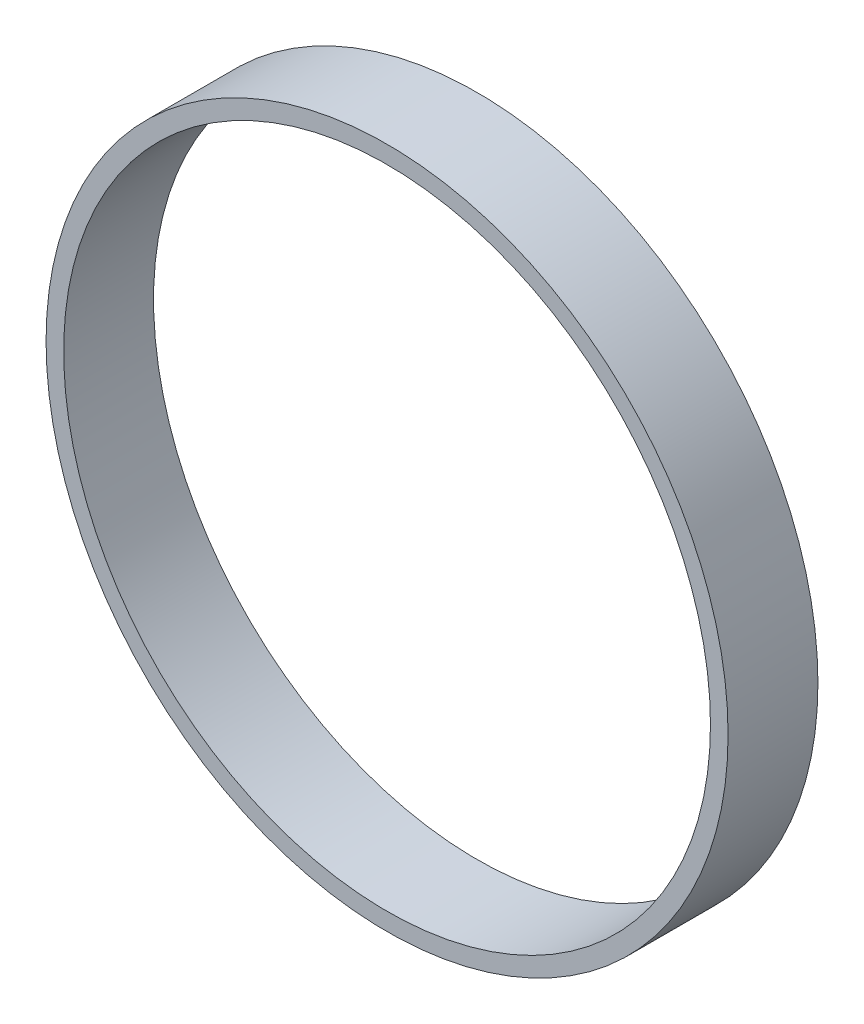
SolidWorks part; units mm, degrees
ref_plane "Front Plane" through (0, 0, 0) normal (0, 0, 1) x (1, 0, 0)
ref_plane "Top Plane" through (0, 0, 0) normal (0, 1, 0) x (1, 0, 0)
ref_plane "Right Plane" through (0, 0, 0) normal (1, 0, 0) x (0, 0, -1)
sketch "Sketch1" plane through (0, 0, 0) normal (0, 0, 1) x (1, 0, 0)
  circle A0 centre (0, 0) radius 37.95
  circle A1 centre (0, 0) radius 35.99
  dimension "D1" = 75.9
  dimension "D2" = 71.98
extrude "Boss-Extrude1" add sketch "Sketch1" along normal blind 10
